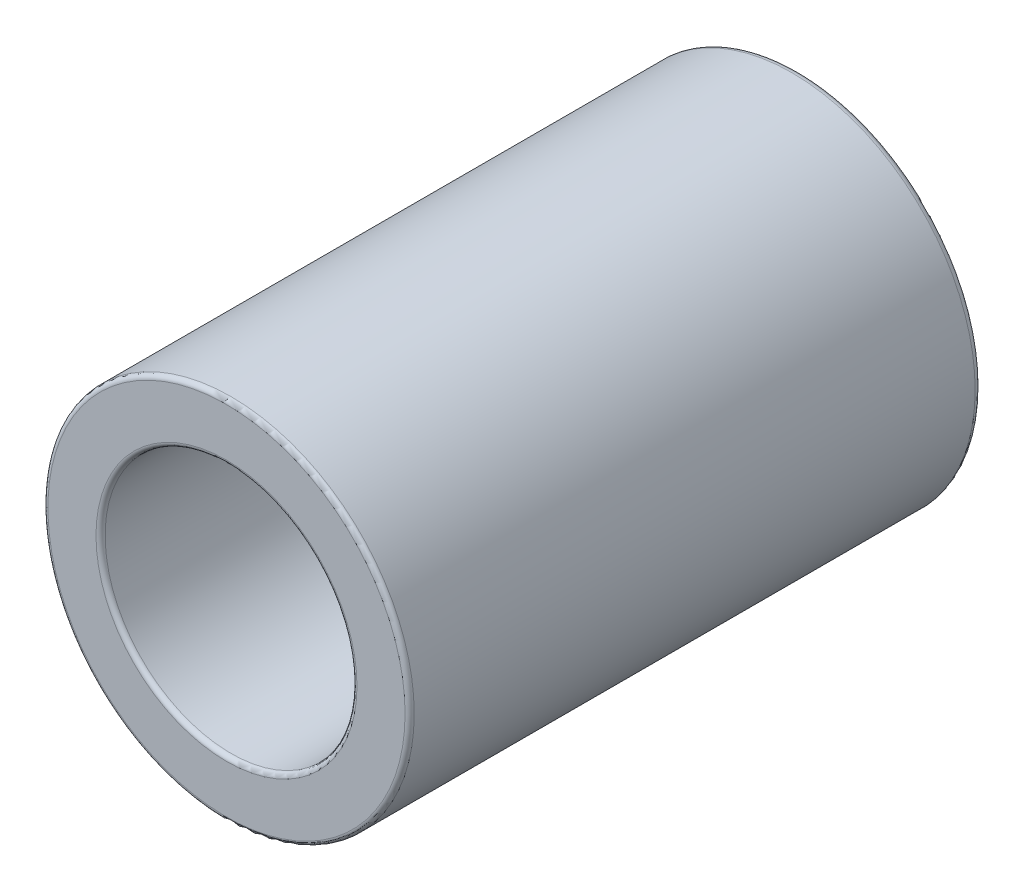
SolidWorks part; units mm, degrees
ref_plane "Front Plane" through (0, 0, 0) normal (0, 0, 1) x (1, 0, 0)
ref_plane "Top Plane" through (0, 0, 0) normal (0, 1, 0) x (1, 0, 0)
ref_plane "Right Plane" through (0, 0, 0) normal (1, 0, 0) x (0, 0, -1)
sketch "Sketch1" plane through (0, 0, 0) normal (0, 0, 1) x (1, 0, 0)
  circle A0 centre (0, 0) radius 8
  dimension "D1" = 16
extrude "Boss-Extrude1" add sketch "Sketch1" along normal blind 25
sketch "Sketch2" plane through (0, 0, 25) normal (0, 0, 1) x (1, 0, 0)
  circle A0 centre (0, 0) radius 5.5
  dimension "D1" = 11
extrude "Cut-Extrude1" cut sketch "Sketch2" against normal blind 20
sketch "Sketch3" plane through (0, 0, 5) normal (0, 0, 1) x (1, 0, 0)
  circle A0 centre (0, 0) radius 2.5
  dimension "D1" = 5
extrude "Cut-Extrude2" cut sketch "Sketch3" against normal through all
fillet "Fillet1" radius 0.2 4 edges at (8, 0, 25) (5.5, 0, 25) (2.5, 0, 0) (2.5, 0, 5)
fillet "Fillet2" radius 0.3 1 edges at (8, 0, 0)
sketch "Sketch4" plane through (0, 0, 0) normal (0, 1, 0) x (1, 0, 0)
  line L0 (0, -29.5962) -> (0, 2.7036) construction
